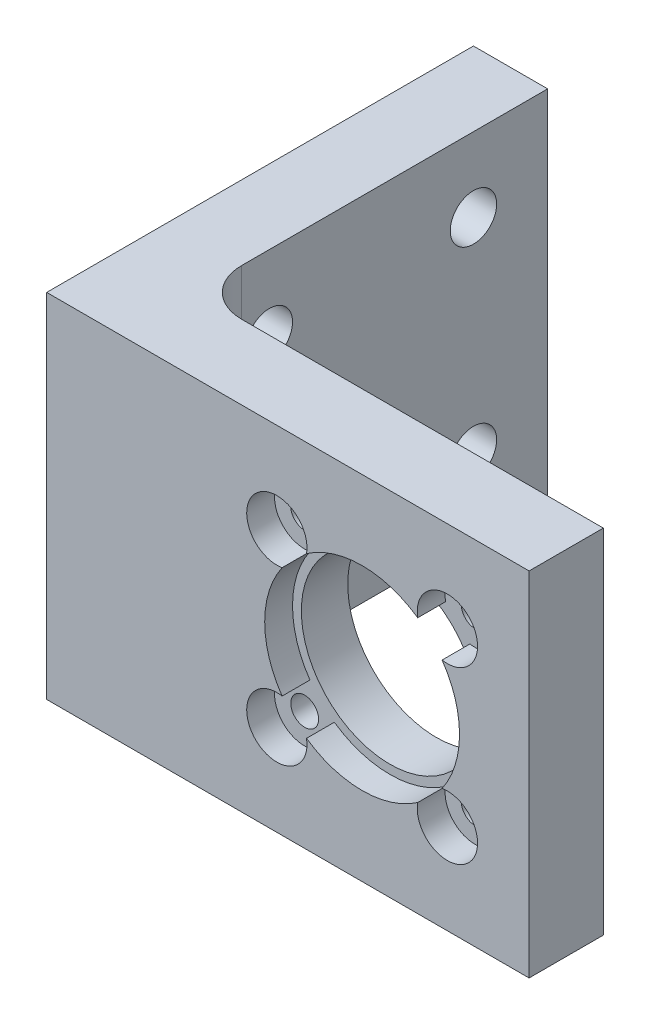
SolidWorks part; units mm, degrees
ref_plane "Piano frontale" through (0, 0, 0) normal (0, 0, 1) x (1, 0, 0)
ref_plane "Piano superiore" through (0, 0, 0) normal (0, 1, 0) x (1, 0, 0)
ref_plane "Piano destro" through (0, 0, 0) normal (1, 0, 0) x (0, 0, -1)
sketch "Sketch1" plane through (0, 0, 0) normal (0, 0, 1) x (1, 0, 0)
  line L0 (0, 19) -> (52, 19) construction
  line L1 (0, 0) -> (52, 0)
  line L2 (0, 0) -> (0, 38)
  line L3 (0, 38) -> (52, 38)
  line L4 (52, 0) -> (52, 38)
  line L5 (26, 38) -> (26, 0) construction
  line L6 (34, 19) -> (43.1924, 28.1924) construction
  line L7 (34, 19) -> (43.1924, 9.8076) construction
  line L8 (34, 19) -> (34, 0) construction
  line L9 (34, 19) -> (24.8076, 9.8076) construction
  line L10 (34, 19) -> (24.8076, 28.1924) construction
  circle A1 centre (34, 19) radius 13 construction
  circle A2 centre (43.1924, 28.1924) radius 1.5
  circle A3 centre (43.1924, 9.8076) radius 1.5
  circle A4 centre (24.8076, 9.8076) radius 1.5
  circle A5 centre (24.8076, 28.1924) radius 1.5
  circle A6 centre (34, 19) radius 9.55
  dimension "D2" = 19.1
  dimension "D4" = 26
  dimension "D6" = 3
  dimension "D7" = 18.3848
  dimension "D9" = 18.3848
  dimension "D1" = 52
  dimension "D3" = 18
  dimension "D5" = 45
  dimension "D8" = 38
  dimension "D10" = 9.1924
extrude "Face_In" add sketch "Sketch1" along normal blind 5
sketch "Sketch8" plane through (0, 0, 0) normal (0, 0, -1) x (-1, 0, 0)
  line L0 (-52, 38) -> (0, 38) construction
  line L1 (-8, 38) -> (0, 38)
  line L3 (-8, 0) -> (0, 0)
  line L6 (0, 38) -> (0, 0) construction
  line L7 (-8, 38) -> (-8, 0)
  line L12 (0, 0) -> (0, 38)
  line L13 (0, 38) -> (-8, 38)
  line L15 (0, 0) -> (-8, 0)
  dimension "D6" = 8
extrude "Bottom" add sketch "Sketch8" along normal blind 38
fillet "Fillet1" radius 5 1 edges at (8, 19, 0)
sketch "Sketch10" plane through (0, 0, 5) normal (0, 0, 1) x (1, 0, 0)
  line L0 (34, 19) -> (34, 38) construction
  line L1 (52, 38) -> (0, 38) construction
  line L2 (34, 19) -> (52, 19) construction
  line L3 (52, 0) -> (52, 38) construction
  line L4 (0, 0) -> (52, 0) construction
  line L9 (0, 38) -> (52, 38)
  line L10 (0, 38) -> (0, 0)
  line L11 (0, 0) -> (52, 0)
  line L12 (52, 38) -> (52, 0)
  line L13 (43.1924, 28.1924) -> (43.1924, 31.4424) construction
  arc A8 (42.6218, 24.9929) -> (39.9929, 27.6218) centre (43.1924, 28.1924) ccw
  arc A9 (25.3782, 24.9929) -> (28.0071, 27.6218) centre (24.8076, 28.1924) cw
  arc A10 (42.6218, 13.0071) -> (39.9929, 10.3782) centre (43.1924, 9.8076) cw
  arc A11 (25.3782, 13.0071) -> (28.0071, 10.3782) centre (24.8076, 9.8076) ccw
  arc A12 (25.3782, 24.9929) -> (25.3782, 13.0071) centre (34, 19) ccw
  arc A13 (39.9929, 27.6218) -> (28.0071, 27.6218) centre (34, 19) ccw
  arc A14 (42.6218, 13.0071) -> (42.6218, 24.9929) centre (34, 19) ccw
  arc A15 (28.0071, 10.3782) -> (39.9929, 10.3782) centre (34, 19) ccw
  point P26 (34, 8.5)
  dimension "D1" = 6.5
  dimension "D2" = 19
  dimension "D4" = 21
  dimension "D3" = 18
  dimension "D5" = 3.25
  dimension "D6" = 10.5
extrude "Face_Out" add sketch "Sketch10" along normal blind 3
sketch "Sketch12" plane through (0, 0, 0) normal (-1, 0, 0) x (0, 0, 1)
  line L0 (0, 0) -> (-38, 38) construction
  line L1 (0, 0) -> (0, 38) construction
  line L2 (-38, 0) -> (0, 38) construction
  line L4 (-19, 19) -> (-19, 0) construction
  line L6 (8, 0) -> (-38, 0) construction
  line L8 (0, 19) -> (-38, 19) construction
  line L9 (-38, 0) -> (-38, 38) construction
  line L10 (-19, 0) -> (-19, 38) construction
  line L11 (8, 38) -> (-38, 38) construction
  line L13 (8, 38) -> (8, 0) construction
  circle A0 centre (-8, 30) radius 2.5
  circle A1 centre (-30, 30) radius 2.5
  circle A2 centre (-8, 8) radius 2.5
  circle A3 centre (-30, 8) radius 2.5
  dimension "D1" = 5
  dimension "D2" = 8
  dimension "D3" = 8
  dimension "D4" = 22
extrude "Screw Holes" cut sketch "Sketch12" against normal blind 8
